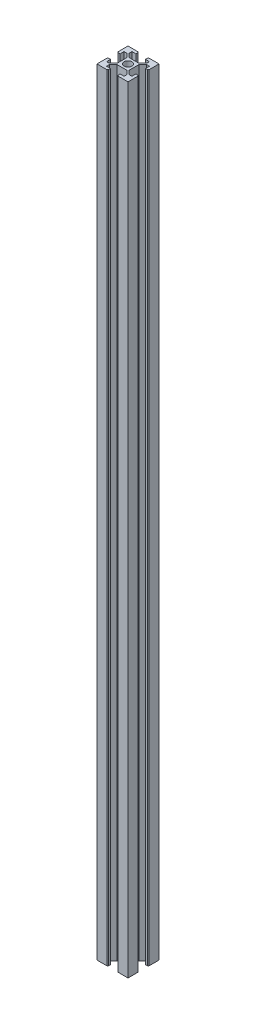
SolidWorks part; units mm, degrees
material "1060 Alloy"
ref_plane "Front Plane" through (0, 0, 0) normal (0, 0, 1) x (1, 0, 0)
ref_plane "Top Plane" through (0, 0, 0) normal (0, 1, 0) x (1, 0, 0)
ref_plane "Right Plane" through (0, 0, 0) normal (1, 0, 0) x (0, 0, -1)
sketch "Sketch1" plane through (0, 0, 0) normal (0, 1, 0) x (1, 0, 0)
  line L0 (3.9, 0) -> (3.9, 3.1)
  line L1 (3.9, 3.1) -> (6.4259, 5.6259)
  line L2 (6.4259, 5.6259) -> (8.1636, 5.6259)
  line L3 (8.1636, 5.6259) -> (8.1636, 3.1)
  line L4 (8.1636, 3.1) -> (9.5, 3.1)
  line L5 (9.5, 3.1) -> (10, 3.6)
  line L6 (10, 3.6) -> (10, 10)
  line L7 (10, 10) -> (3.6, 10)
  line L8 (3.6, 10) -> (3.1, 9.5)
  line L9 (3.1, 9.5) -> (3.1, 8.1636)
  line L10 (3.1, 8.1636) -> (5.6259, 8.1636)
  line L11 (5.6259, 8.1636) -> (5.6259, 6.4259)
  line L12 (5.6259, 6.4259) -> (3.1, 3.9)
  line L13 (3.1, 3.9) -> (0, 3.9)
  line L14 (0, 3.9) -> (0, -3.9) construction
  line L15 (-22.3798, 0) -> (39.9474, 0) construction
  line L16 (0, -3.9) -> (3.1, -3.9)
  line L17 (3.1, -3.9) -> (5.6259, -6.4259)
  line L18 (5.6259, -6.4259) -> (5.6259, -8.1636)
  line L19 (5.6259, -8.1636) -> (3.1, -8.1636)
  line L20 (3.1, -8.1636) -> (3.1, -9.5)
  line L21 (3.1, -9.5) -> (3.6, -10)
  line L22 (3.6, -10) -> (10, -10)
  line L23 (10, -10) -> (10, -3.6)
  line L24 (10, -3.6) -> (9.5, -3.1)
  line L25 (9.5, -3.1) -> (8.1636, -3.1)
  line L26 (8.1636, -3.1) -> (8.1636, -5.6259)
  line L27 (8.1636, -5.6259) -> (6.4259, -5.6259)
  line L28 (6.4259, -5.6259) -> (3.9, -3.1)
  line L29 (3.9, -3.1) -> (3.9, 0)
  line L30 (-3.9, 0) -> (-3.9, -3.1)
  line L31 (-3.9, -3.1) -> (-6.4259, -5.6259)
  line L32 (-6.4259, -5.6259) -> (-8.1636, -5.6259)
  line L33 (-8.1636, -5.6259) -> (-8.1636, -3.1)
  line L34 (-8.1636, -3.1) -> (-9.5, -3.1)
  line L35 (-9.5, -3.1) -> (-10, -3.6)
  line L36 (-10, -3.6) -> (-10, -10)
  line L37 (-10, -10) -> (-3.6, -10)
  line L38 (-3.6, -10) -> (-3.1, -9.5)
  line L39 (-3.1, -9.5) -> (-3.1, -8.1636)
  line L40 (-3.1, -8.1636) -> (-5.6259, -8.1636)
  line L41 (-5.6259, -8.1636) -> (-5.6259, -6.4259)
  line L42 (-5.6259, -6.4259) -> (-3.1, -3.9)
  line L43 (-3.1, -3.9) -> (0, -3.9)
  line L44 (0, 3.9) -> (-3.1, 3.9)
  line L45 (-3.1, 3.9) -> (-5.6259, 6.4259)
  line L46 (-5.6259, 6.4259) -> (-5.6259, 8.1636)
  line L47 (-5.6259, 8.1636) -> (-3.1, 8.1636)
  line L48 (-3.1, 8.1636) -> (-3.1, 9.5)
  line L49 (-3.1, 9.5) -> (-3.6, 10)
  line L50 (-3.6, 10) -> (-10, 10)
  line L51 (-10, 10) -> (-10, 3.6)
  line L52 (-10, 3.6) -> (-9.5, 3.1)
  line L53 (-9.5, 3.1) -> (-8.1636, 3.1)
  line L54 (-8.1636, 3.1) -> (-8.1636, 5.6259)
  line L55 (-8.1636, 5.6259) -> (-6.4259, 5.6259)
  line L56 (-6.4259, 5.6259) -> (-3.9, 3.1)
  line L57 (-3.9, 3.1) -> (-3.9, 0)
  circle A0 centre (0, 0) radius 2.5
  point P70 (0, 0)
  dimension "D1" = 5
  dimension "D2" = 6.1
  dimension "D4" = 20
  dimension "D5" = 135
  dimension "D6" = 3.6
  dimension "D7" = 3.1
  dimension "D3" = 4
extrude "Boss-Extrude1" add sketch "Sketch1" along normal blind 500 contours L56 L57 L30 L31 L32 L33 L34 L35 L36 L37 L38 L39 L40 L41 L42 L43 L16 L17 L18 L19 L20 L21 L22 L23 L24 L25 L26 L27 L28 L29 L0 L1 L2 L3 L4 L5 L6 L7 L8 L9 L10 L11 L12 L13 L44 L45 L46 L47 L48 L49 L50
